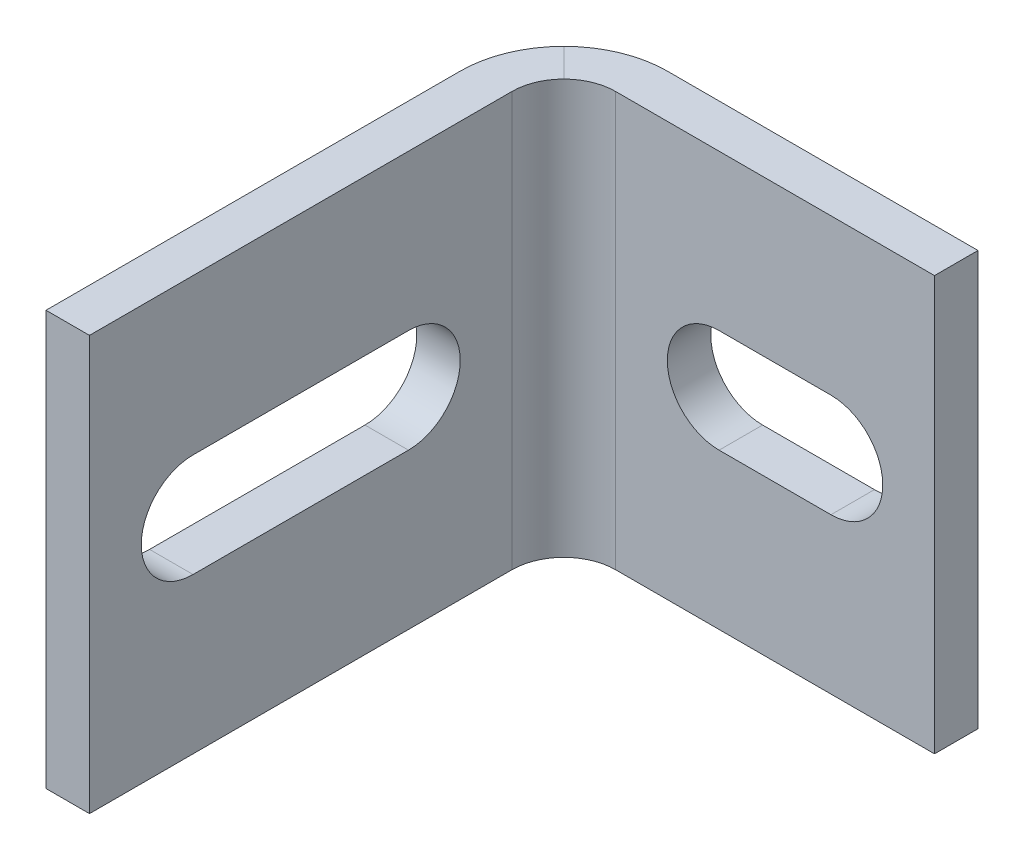
SolidWorks part; units mm, degrees
ref_plane "Front Plane" through (0, 0, 0) normal (0, 0, 1) x (1, 0, 0)
ref_plane "Top Plane" through (0, 0, 0) normal (0, 1, 0) x (1, 0, 0)
ref_plane "Right Plane" through (0, 0, 0) normal (1, 0, 0) x (0, 0, -1)
sketch "Sketch1" plane through (0, 0, 0) normal (0, 0, 1) x (1, 0, 0)
  line L0 (0, 12.7) -> (0, -12.7)
  line L1 (0, 0) -> (2.667, 0)
  point P4 (0, 0)
  point P8 (0, 0)
  point P9 (0, 0)
sketch "Sketch2" plane through (0, 0, 0) normal (0, 1, 0) x (1, 0, 0)
  line L0 (0, 0) -> (0, 28.575)
  line L1 (3.175, 31.75) -> (25.4, 31.75)
  arc A0 (3.175, 31.75) -> (0, 28.575) centre (3.175, 28.575) ccw
  point P6 (0, 31.75)
sketch "Sketch3" plane through (0, 0, 0) normal (0, 0, 1) x (1, 0, 0)
  line L8 (2.667, -12.7) -> (0, -12.7)
  line L9 (2.667, -12.7) -> (2.667, 12.7)
  line L10 (0, -12.7) -> (0, 12.7)
  line L11 (2.667, 12.7) -> (0, 12.7)
  line L12 (2.667, -12.7) -> (0, 12.7) construction
  line L13 (0, -12.7) -> (2.667, 12.7) construction
  line L14 (0, 0) -> (2.667, 0) construction
  point P1 (0, 0)
  point P2 (1.3335, 0)
  dimension "D1" = 2.667
  dimension "D2" = 25.4
  dimension "D3" = 12.7
sketch "Sketch4" plane through (0, 0, 0) normal (0, 1, 0) x (1, 0, 0)
  line L0 (0, 0) -> (0, 31.75)
  line L1 (0, 31.75) -> (25.4, 31.75)
  dimension "D2" = 25.4
  dimension "D1" = 31.75
sweep "Sweep1" add profiles "Sketch3" path "Sketch4"
fillet "Fillet1" radius 3.175 1 edges at (2.667, 0, -29.083)
fillet "Fillet2" radius 6.35 1 edges at (0, 0, -31.75)
sketch "Sketch5" plane through (0, 0, 0) normal (1, 0, 0) x (0, 0, -1)
  line L0 (0, 0) -> (25.908, 0) construction
  line L1 (25.908, -12.7) -> (25.908, 12.7) construction
  line L2 (12.954, 3.175) -> (12.954, -3.175)
  point P8 (12.954, 0)
sketch "Sketch6" plane through (0, 0, 0) normal (1, 0, 0) x (0, 0, -1)
  line L0 (0, 0) -> (25.908, 0) construction
  line L1 (25.908, -12.7) -> (25.908, 12.7) construction
  line L2 (19.558, 0) -> (6.35, 0) construction
  line L3 (19.558, -3.175) -> (6.35, -3.175)
  line L4 (19.558, 3.175) -> (6.35, 3.175)
  arc A0 (19.558, -3.175) -> (19.558, 3.175) centre (19.558, 0) ccw
  arc A1 (6.35, 3.175) -> (6.35, -3.175) centre (6.35, 0) ccw
  point P7 (12.954, 0)
  point P12 (3.175, 0)
  dimension "D1" = 3.175
  dimension "D2" = 6.35
extrude "Cut-Extrude2" cut sketch "Sketch6" along normal up to next
sketch "Sketch7" plane through (0, 0, -29.083) normal (0, 0, 1) x (1, 0, 0)
  line L0 (25.4, 0) -> (5.842, 0) construction
  line L1 (25.4, -12.7) -> (25.4, 12.7) construction
  line L2 (5.842, 12.7) -> (5.842, -12.7) construction
  line L3 (12.192, 0) -> (19.05, 0) construction
  line L4 (12.192, 3.175) -> (19.05, 3.175)
  line L5 (12.192, -3.175) -> (19.05, -3.175)
  arc A0 (12.192, 3.175) -> (12.192, -3.175) centre (12.192, 0) ccw
  arc A1 (19.05, -3.175) -> (19.05, 3.175) centre (19.05, 0) ccw
  point P8 (15.621, 0)
  point P13 (22.225, 0)
  dimension "D1" = 3.175
  dimension "D2" = 6.35
extrude "Cut-Extrude3" cut sketch "Sketch7" against normal through all
equation "\"D1@Sketch3\"=\"Thickness@Sketch1\""
equation "\"D2@Sketch3\"=\"LengthC@Sketch1\""
equation "\"D3@Sketch3\"=\"LengthC@Sketch1\"/2"
equation "\"D1@Sketch4\"=\"LengthA@Sketch2\""
equation "\"D2@Sketch4\"=\"LengthB@Sketch2\""
equation "\"D1@Fillet1\"=\"CornerRadius@Sketch2\""
equation "\"D1@Fillet2\"=\"CornerRadius@Sketch2\"*2"
equation "\"D2@Sketch6\"=\"ScrewSize@Sketch5\""
equation "\"D2@Sketch7\"=\"ScrewSize@Sketch5\""
